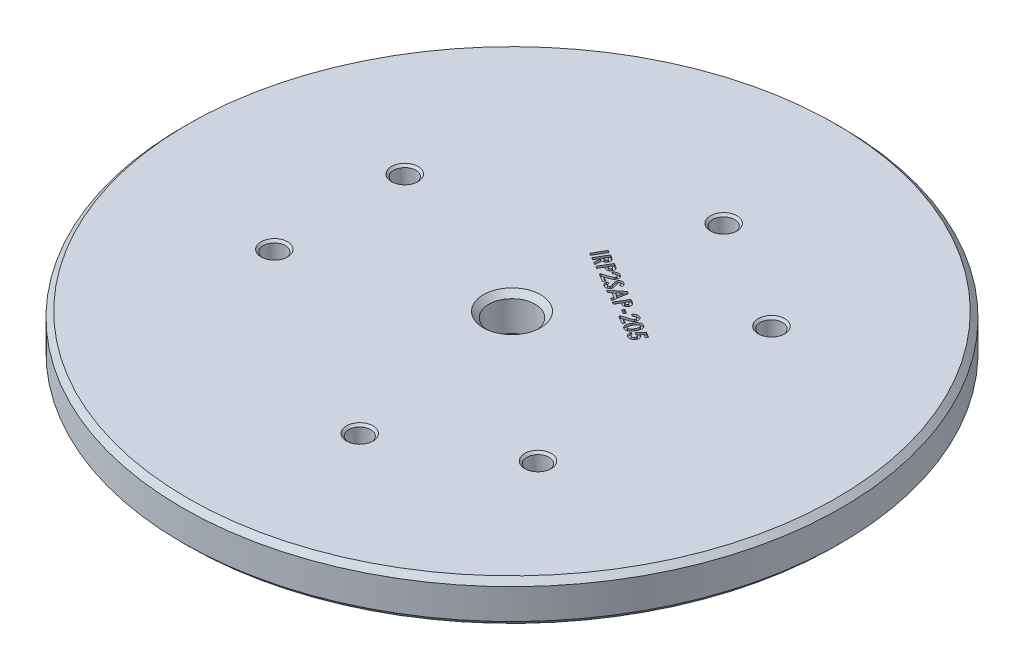
SolidWorks part; units mm, degrees
material "6061-T6 (SS)"
ref_plane "Front" through (0, 0, 0) normal (0, 0, 1) x (1, 0, 0)
ref_plane "Top" through (0, 0, 0) normal (0, 1, 0) x (1, 0, 0)
ref_plane "Right" through (0, 0, 0) normal (1, 0, 0) x (0, 0, -1)
sketch "Sketch1" plane through (0, 0, 0) normal (0, 0, 1) x (1, 0, 0)
  line L0 (-0.9928, 4.6579) -> (275.8281, 63.6587)
  line L1 (0.9928, -4.6579) -> (276.8319, 54.1337)
  line L2 (276.8319, 54.1337) -> (427.2243, 54.1337)
  line L3 (275.8281, 63.6587) -> (428.2281, 63.6587)
  line L4 (428.2281, 63.6587) -> (705.049, 4.6579)
  line L5 (703.0635, -4.6579) -> (427.2243, 54.1337)
  line L6 (0, 0) -> (352.0281, 63.6587) construction
  line L7 (352.0281, 63.6587) -> (704.0562, 0) construction
  line L8 (352.0281, 63.6587) -> (352.0281, 54.1337) construction
  line L9 (275.8281, 63.6587) -> (276.8319, 54.1337)
  line L10 (428.2281, 63.6587) -> (427.2243, 54.1337)
  circle A0 centre (0, 0) radius 6.985
  circle A1 centre (704.0562, 0) radius 6.985
  circle A2 centre (0, 0) radius 4.7625
  circle A3 centre (704.0562, 0) radius 4.7625
  point P15 (352.0281, 54.1337)
  dimension "D2" = 13.97
  dimension "D3" = 9.525
  dimension "D1" = 704.0562
  dimension "D4" = 9.525
  dimension "D5" = 152.4
  dimension "D6" = 63.6587
extrude "Boss-Extrude1" add sketch "Sketch1" along normal mid plane 152.4 contours L10 L3 L9 L2
sketch "Sketch13" plane through (0, 54.1337, 0) normal (0, -1, 0) x (1, 0, 0)
  line L0 (276.8319, -76.2) -> (427.2243, -76.2) construction
  line L1 (276.8319, 76.2) -> (275.8281, 76.2)
  line L2 (276.8319, 76.2) -> (276.8319, -76.2)
  line L3 (276.8319, -76.2) -> (275.8281, -76.2)
  line L4 (275.8281, 76.2) -> (275.8281, -76.2)
  line L5 (427.2243, 76.2) -> (428.2281, 76.2)
  line L6 (427.2243, 76.2) -> (427.2243, -76.2)
  line L7 (427.2243, -76.2) -> (428.2281, -76.2)
  line L8 (428.2281, 76.2) -> (428.2281, -76.2)
  point P10 (427.2243, -69.4903)
  point P13 (0, 0)
  dimension "D1" = 152.4
extrude "Boss-Extrude2" add sketch "Sketch13" against normal up to surface (9.525 mm away) up to face at (352.0281, 63.6587, 0)
sketch "Sketch3" plane through (0, 63.6587, 0) normal (0, 1, 0) x (1, 0, 0)
  line L0 (385.0237, -26.9875) -> (358.9022, -42.0688) construction
  line L1 (358.9022, -42.0688) -> (312.1585, -15.0812) construction
  line L2 (312.1585, -15.0812) -> (312.1585, 15.0812) construction
  line L3 (312.1585, 15.0812) -> (358.9022, 42.0688) construction
  line L4 (358.9022, 42.0688) -> (385.0237, 26.9875) construction
  line L5 (385.0237, 26.9875) -> (385.0237, -26.9875) construction
  line L6 (385.0237, -26.9875) -> (385.0237, -57.15) construction
  line L7 (385.0237, -57.15) -> (358.9022, -42.0688) construction
  line L8 (312.1585, -15.0812) -> (286.037, 0) construction
  line L9 (286.037, 0) -> (312.1585, 15.0812) construction
  line L10 (358.9022, 42.0688) -> (385.0237, 57.15) construction
  line L11 (385.0237, 57.15) -> (385.0237, 26.9875) construction
  line L12 (312.1585, 0) -> (352.0281, 0) construction
  line L13 (352.0281, 0) -> (371.9629, 34.5281) construction
  line L14 (352.0281, 0) -> (371.9629, -34.5281) construction
  line L15 (275.8281, 0) -> (352.0281, 0) construction
  line L16 (428.2281, -76.2) -> (428.2281, 76.2) construction
  line L17 (352.0281, 0) -> (428.2281, 0) construction
  line L18 (275.8281, -76.2) -> (275.8281, 76.2) construction
  circle A0 centre (312.1585, -15.0812) radius 3.4925 construction
  circle A1 centre (312.1585, 15.0812) radius 3.4925 construction
  circle A2 centre (358.9022, 42.0688) radius 3.4925 construction
  circle A3 centre (385.0237, 26.9875) radius 3.4925 construction
  circle A4 centre (385.0237, -26.9875) radius 3.4925 construction
  circle A5 centre (358.9022, -42.0688) radius 3.4925 construction
  point P23 (0, 0)
  point P24 (0, 0)
  dimension "D3" = 6.985
  dimension "D1" = 30.1625
  dimension "D2" = 53.975
hole_wizard "1/4-20 Tapped Hole1" positions "Sketch4" profile "Sketch5" tap size "1/4-20" standard "ANSI Inch" end condition through all
sketch "Sketch4" plane through (0, 63.6587, 0) normal (0, 1, 0) x (1, 0, 0)
  point P0 (312.1585, -15.0812)
  point P3 (312.1585, 15.0812)
  point P6 (358.9022, 42.0688)
  point P9 (385.0237, 26.9875)
  point P12 (385.0237, -26.9875)
  point P15 (358.9022, -42.0688)
sketch "Sketch5" plane through (312.1585, 63.6587, 15.0812) normal (1, 0, 0) x (0, 0, 1)
  line L0 (0, 0) -> (0, 9.525)
  line L1 (0, 9.525) -> (2.5527, 9.525)
  line L2 (2.5527, 9.525) -> (2.5527, 0)
  line L5 (2.5527, 0) -> (0, 0)
  line L11 (0, -6.35) -> (0, 107.95) construction
  dimension "Thru Tap Drill Dia." = 5.1054
  dimension "Thru Tap Drill Depth" = 9.525
cosmetic thread "Hole Thread1" parameters "D2"=6.35
cosmetic thread "Hole Thread2" parameters "D2"=6.35
cosmetic thread "Hole Thread3" parameters "D2"=6.35
cosmetic thread "Hole Thread4" parameters "D2"=6.35
cosmetic thread "Hole Thread5" parameters "D2"=6.35
cosmetic thread "Hole Thread6" parameters "D2"=6.35
chamfer "Chamfer2" distance 0.508 angle 45 12 edges at (385.0237, 54.1337, -24.4348) (385.0237, 63.6587, -24.4348) (358.9022, 54.1337, -39.5161) (358.9022, 63.6587, -39.516) (385.0237, 54.1337, 29.5402) (385.0237, 63.6587, 29.5402) (358.9022, 54.1337, 44.6214) (358.9022, 63.6587, 44.6215) (312.1585, 54.1337, -12.5286) (312.1585, 63.6587, -12.5285) (312.1585, 54.1337, 17.6339) (312.1585, 63.6587, 17.634)
sketch "Sketch12" plane through (0, 63.6587, 0) normal (0, 1, 0) x (1, 0, 0)
  line L0 (275.8281, 76.2) -> (428.2281, 76.2) construction
  line L1 (275.8281, -76.2) -> (428.2281, -76.2) construction
  line L7 (428.2281, 76.2) -> (275.8281, 76.2)
  line L8 (428.2281, -76.2) -> (428.2281, 76.2)
  line L9 (275.8281, -76.2) -> (428.2281, -76.2)
  line L10 (428.2281, -76.2) -> (428.2281, 76.2)
  line L11 (428.2281, 76.2) -> (275.8281, 76.2)
  line L13 (275.8281, -76.2) -> (428.2281, -76.2)
  line L15 (275.8281, 76.2) -> (275.8281, -76.2)
  line L16 (275.8281, 76.2) -> (275.8281, -76.2)
  circle A0 centre (352.0281, 0) radius 76.2
  dimension "D1" = 0
extrude "Cut-Extrude4" cut sketch "Sketch12" against normal through all
hole_wizard "1/2-13 Tapped Hole1" positions "Sketch9" profile "Sketch11" tap size "1/2-13" standard "ANSI Inch" end condition through all
sketch "Sketch9" plane through (0, 63.6587, 0) normal (0, 1, 0) x (1, 0, 0)
  circle A0 centre (352.0281, 0) radius 76.2 construction
  point P0 (352.0281, 0)
  point P3 (0, 0)
  point P11 (0, 0)
sketch "Sketch11" plane through (352.0281, 63.6587, 0) normal (1, 0, 0) x (0, 0, 1)
  line L0 (0, 0) -> (0, 9.525)
  line L1 (0, 9.525) -> (5.3581, 9.525)
  line L2 (5.3581, 9.525) -> (5.3581, 0)
  line L5 (5.3581, 0) -> (0, 0)
  line L11 (0, -6.35) -> (0, 107.95) construction
  dimension "Thru Tap Drill Dia." = 10.7163
  dimension "Thru Tap Drill Depth" = 9.525
cosmetic thread "Hole Thread7" parameters "D2"=12.7
chamfer "Chamfer3" distance 1.27 angle 45 4 edges at (352.0281, 63.6587, 5.3581) (352.0281, 54.1337, 5.3581) (352.0281, 63.6587, 76.2) (352.0281, 54.1337, 76.2)
sketch "Sketch7" plane through (0, 63.6587, 0) normal (0, 1, 0) x (1, 0, 0)
  line L0 (358.9022, 42.0688) -> (312.1585, 15.0812) construction
  line L1 (312.1585, 15.0812) -> (385.0237, -26.9875) construction
  line L2 (385.0237, -26.9875) -> (385.0237, 26.9875) construction
  line L3 (335.5303, 28.575) -> (385.0237, 0) construction
  text T0 "<b>IRP2SAP-205</b>"
extrude "Cut-Extrude2" cut sketch "Sketch7" against normal blind 0.508
sketch "Sketch8" plane through (0, 54.1337, 0) normal (0, -1, 0) x (1, 0, 0)
  line L0 (385.0237, -26.9875) -> (385.0237, 26.9875) construction
  line L1 (385.0237, 26.9875) -> (312.1585, -15.0812) construction
  line L2 (312.1585, -15.0812) -> (358.9022, -42.0688) construction
  line L3 (358.9022, -42.0688) -> (385.0237, 0) construction
  line L4 (385.0237, 0) -> (335.5303, -28.575) construction
  text T0 "<b>IRP2SAP-205</b>"
extrude "Cut-Extrude3" cut sketch "Sketch8" against normal blind 0.508
